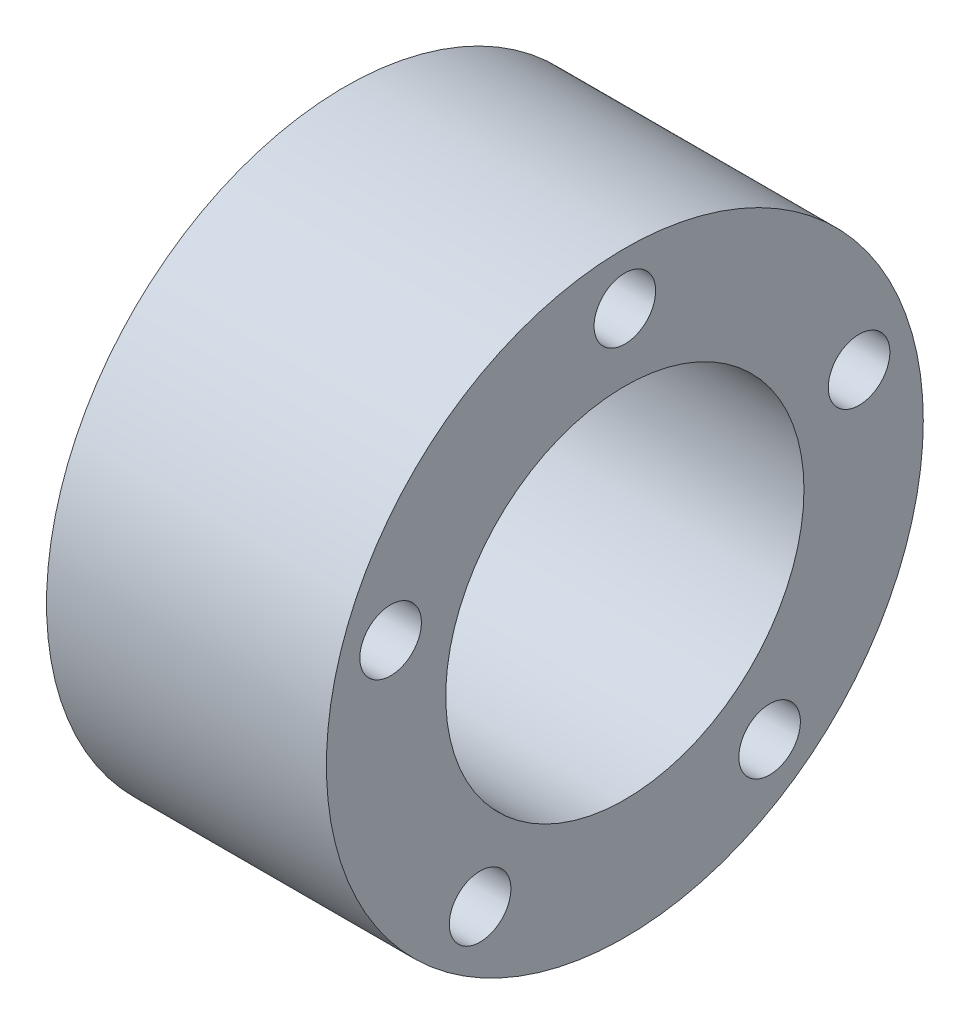
SolidWorks part; units mm, degrees
material "6061 Alloy"
ref_plane "Front Plane" through (0, 0, 0) normal (0, 0, 1) x (1, 0, 0)
ref_plane "Top Plane" through (0, 0, 0) normal (0, 1, 0) x (1, 0, 0)
ref_plane "Right Plane" through (0, 0, 0) normal (1, 0, 0) x (0, 0, -1)
sketch "Sketch1" plane through (0, 0, 0) normal (1, 0, 0) x (0, 0, -1)
  circle A0 centre (0, 0) radius 13.5435
  circle A1 centre (0, 0) radius 8.128
  dimension "D1" = 16.256
  dimension "D2" = 27.0869
extrude "Boss-Extrude1" add sketch "Sketch1" along normal blind 12.7
sketch "Sketch2" plane through (0, 0, 0) normal (-1, 0, 0) x (0, 0, 1)
  line L0 (0, 0) -> (0, 11.176) construction
  circle A0 centre (0, 11.176) radius 1.397
  circle A1 centre (10.629, 3.4536) radius 1.397
  circle A2 centre (6.5691, -9.0416) radius 1.397
  circle A3 centre (-6.5691, -9.0416) radius 1.397
  circle A4 centre (-10.629, 3.4536) radius 1.397
  point P14 (0, 0)
  dimension "D1" = 5
  dimension "D2" = 2.794
  dimension "D3" = 11.176
extrude "Cut-Extrude1" cut sketch "Sketch2" against normal through all
sketch "Sketch3" [suppressed] plane through (0, 0, 0) normal (0, 1, 0) x (1, 0, 0)
  line L0 (0, 0) -> (10.16, 0) construction
  line L1 (0, 13.9245) -> (0, -13.9245) construction
  line L2 (10.16, -13.9245) -> (10.16, 13.9245) construction
  circle A0 centre (5.08, 0) radius 1.397
  dimension "D1" = 2.794
extrude "Cut-Extrude2" [suppressed] cut sketch "Sketch3" against normal through all
